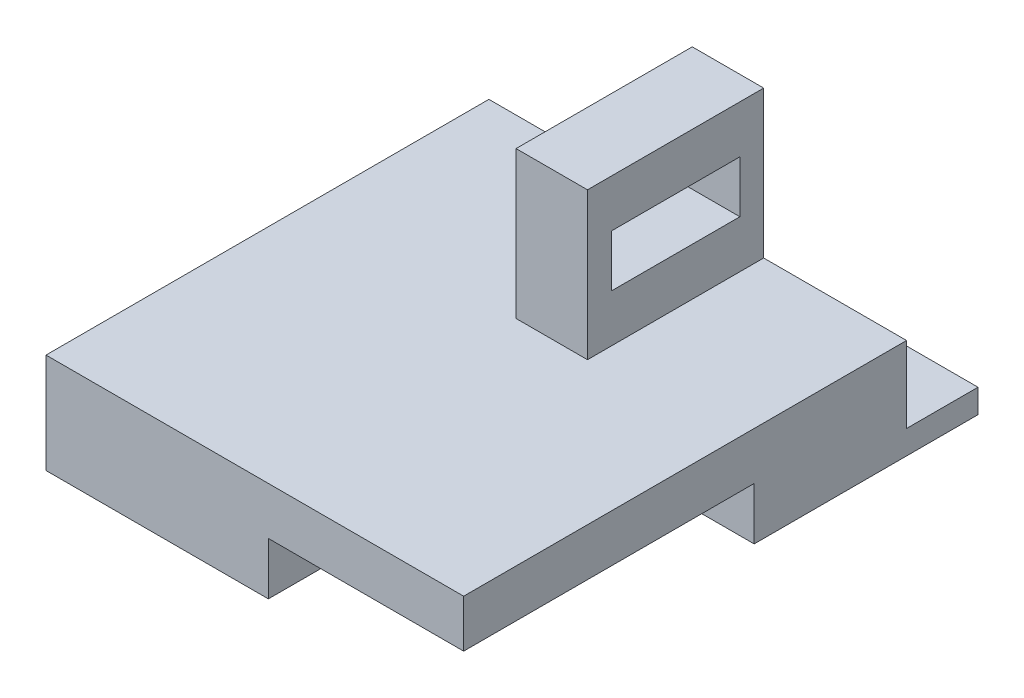
SolidWorks part; units mm, degrees
ref_plane "Front Plane" through (0, 0, 0) normal (0, 0, 1) x (1, 0, 0)
ref_plane "Top Plane" through (0, 0, 0) normal (0, 1, 0) x (1, 0, 0)
ref_plane "Right Plane" through (0, 0, 0) normal (1, 0, 0) x (0, 0, -1)
sketch "Sketch1" plane through (0, 0, 0) normal (0, 1, 0) x (1, 0, 0)
  line L1 (0, 0) -> (87.7, 0)
  line L2 (0, 0) -> (0, 108)
  line L3 (0, 108) -> (87.7, 108)
  line L4 (87.7, 0) -> (87.7, 108)
extrude "Boss-Extrude1" add sketch "Sketch1" along normal blind 21
sketch "Sketch2" plane through (0, 0, 0) normal (0, -1, 0) x (-1, 0, 0)
  line L1 (-87.7, 0) -> (-46.692, 0)
  line L2 (-87.7, 0) -> (-87.7, 61)
  line L3 (-87.7, 61) -> (-46.692, 61)
  line L4 (-46.692, 0) -> (-46.692, 61)
extrude "Cut-Extrude1" cut sketch "Sketch2" against normal blind 11
ref_plane "Plane1" through (87.7, 11, -61) normal (0, -1, 0) x (-1, 0, 0)
sketch "Sketch5" plane through (0, 21, 0) normal (0, 1, 0) x (1, 0, 0)
  line L0 (87.7, 0) -> (87.7, 108) construction
  line L1 (0, 108) -> (87.7, 108)
  line L2 (0, 108) -> (0, 93)
  line L3 (0, 93) -> (87.7, 93)
  line L4 (87.7, 108) -> (87.7, 93)
extrude "Cut-Extrude2" cut sketch "Sketch5" against normal blind 16
ref_plane "Plane2" through (87.7, 0, -108) normal (0, -1, 0) x (-1, 0, 0)
sketch "Sketch7" plane through (0, 21, 0) normal (0, 1, 0) x (1, 0, 0)
  line L5 (57.7, 93) -> (42.7, 93)
  line L6 (57.7, 93) -> (57.7, 56)
  line L7 (57.7, 56) -> (42.7, 56)
  line L8 (42.7, 93) -> (42.7, 56)
extrude "Boss-Extrude2" add sketch "Sketch7" along normal blind 30.9
sketch "Sketch8" plane through (57.7, 0, 0) normal (1, 0, 0) x (0, 0, -1)
  line L1 (88, 31) -> (61, 31)
  line L2 (88, 31) -> (88, 41.9)
  line L3 (88, 41.9) -> (61, 41.9)
  line L4 (61, 31) -> (61, 41.9)
extrude "Cut-Extrude3" cut sketch "Sketch8" against normal blind 30.9
